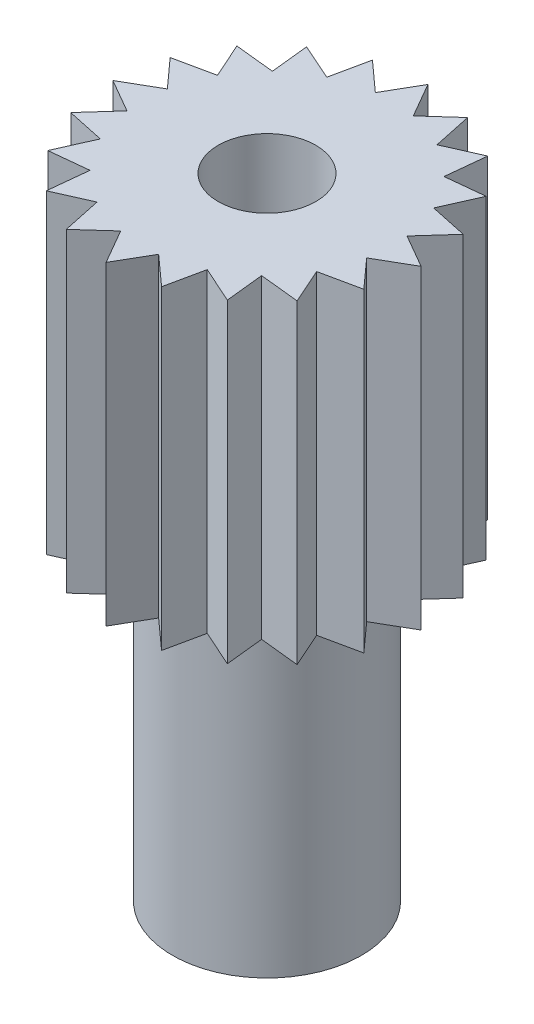
SolidWorks part; units mm, degrees
ref_plane "Front Plane" through (0, 0, 0) normal (0, 0, 1) x (1, 0, 0)
ref_plane "Top Plane" through (0, 0, 0) normal (0, 1, 0) x (1, 0, 0)
ref_plane "Right Plane" through (0, 0, 0) normal (1, 0, 0) x (0, 0, -1)
sketch "Sketch1" plane through (0, 0, 0) normal (0, 1, 0) x (1, 0, 0)
  circle A0 centre (0, 0) radius 3
  circle A1 centre (0, 0) radius 7
extrude "Boss-Extrude1" add sketch "Sketch1" along normal blind 20
sketch "Sketch2" plane through (0, 20, 0) normal (0, 1, 0) x (1, 0, 0)
  circle A0 centre (0, 0) radius 10
  circle A1 centre (0, 0) radius 3
extrude "Boss-Extrude2" add sketch "Sketch2" along normal blind 20
sketch "Sketch3" plane through (0, 40, 0) normal (0, 1, 0) x (1, 0, 0)
  line L0 (3.2961, 9.4437) -> (1.3653, 7.7052)
  line L1 (0.2165, 10) -> (-1.0825, 7.75)
  line L2 (-1.0825, 7.75) -> (1.5155, 7.75)
  line L3 (1.5155, 7.75) -> (0.2165, 10)
  line L4 (3.8363, 6.9024) -> (3.2961, 9.4437)
  line L5 (1.3653, 7.7052) -> (3.8363, 6.9024)
  line L6 (6.053, 7.9629) -> (3.6795, 6.9062)
  line L7 (5.7814, 5.3791) -> (6.053, 7.9629)
  line L8 (3.6795, 6.9062) -> (5.7814, 5.3791)
  line L9 (8.2174, 5.7027) -> (5.6336, 5.4311)
  line L10 (7.1607, 3.3292) -> (8.2174, 5.7027)
  line L11 (5.6336, 5.4311) -> (7.1607, 3.3292)
  line L12 (9.5775, 2.8843) -> (7.0362, 3.4244)
  line L13 (7.839, 0.9535) -> (9.5775, 2.8843)
  line L14 (7.0362, 3.4244) -> (7.839, 0.9535)
  line L15 (10, -0.2165) -> (7.75, 1.0825)
  line L16 (7.75, -1.5155) -> (10, -0.2165)
  line L17 (7.75, 1.0825) -> (7.75, -1.5155)
  line L18 (9.4437, -3.2961) -> (7.7052, -1.3653)
  line L19 (6.9024, -3.8363) -> (9.4437, -3.2961)
  line L20 (7.7052, -1.3653) -> (6.9024, -3.8363)
  line L21 (7.9629, -6.053) -> (6.9062, -3.6795)
  line L22 (5.3791, -5.7814) -> (7.9629, -6.053)
  line L23 (6.9062, -3.6795) -> (5.3791, -5.7814)
  line L24 (5.7027, -8.2174) -> (5.4311, -5.6336)
  line L25 (3.3292, -7.1607) -> (5.7027, -8.2174)
  line L26 (5.4311, -5.6336) -> (3.3292, -7.1607)
  line L27 (2.8843, -9.5775) -> (3.4244, -7.0362)
  line L28 (0.9535, -7.839) -> (2.8843, -9.5775)
  line L29 (3.4244, -7.0362) -> (0.9535, -7.839)
  line L30 (-0.2165, -10) -> (1.0825, -7.75)
  line L31 (-1.5155, -7.75) -> (-0.2165, -10)
  line L32 (1.0825, -7.75) -> (-1.5155, -7.75)
  line L33 (-3.2961, -9.4437) -> (-1.3653, -7.7052)
  line L34 (-3.8363, -6.9024) -> (-3.2961, -9.4437)
  line L35 (-1.3653, -7.7052) -> (-3.8363, -6.9024)
  line L36 (-6.053, -7.9629) -> (-3.6795, -6.9062)
  line L37 (-5.7814, -5.3791) -> (-6.053, -7.9629)
  line L38 (-3.6795, -6.9062) -> (-5.7814, -5.3791)
  line L39 (-8.2174, -5.7027) -> (-5.6336, -5.4311)
  line L40 (-7.1607, -3.3292) -> (-8.2174, -5.7027)
  line L41 (-5.6336, -5.4311) -> (-7.1607, -3.3292)
  line L42 (-9.5775, -2.8843) -> (-7.0362, -3.4244)
  line L43 (-7.839, -0.9535) -> (-9.5775, -2.8843)
  line L44 (-7.0362, -3.4244) -> (-7.839, -0.9535)
  line L45 (-10, 0.2165) -> (-7.75, -1.0825)
  line L46 (-7.75, 1.5155) -> (-10, 0.2165)
  line L47 (-7.75, -1.0825) -> (-7.75, 1.5155)
  line L48 (-9.4437, 3.2961) -> (-7.7052, 1.3653)
  line L49 (-6.9024, 3.8363) -> (-9.4437, 3.2961)
  line L50 (-7.7052, 1.3653) -> (-6.9024, 3.8363)
  line L51 (-7.9629, 6.053) -> (-6.9062, 3.6795)
  line L52 (-5.3791, 5.7814) -> (-7.9629, 6.053)
  line L53 (-6.9062, 3.6795) -> (-5.3791, 5.7814)
  line L54 (-5.7027, 8.2174) -> (-5.4311, 5.6336)
  line L55 (-3.3292, 7.1607) -> (-5.7027, 8.2174)
  line L56 (-5.4311, 5.6336) -> (-3.3292, 7.1607)
  line L57 (-2.8843, 9.5775) -> (-3.4244, 7.0362)
  line L58 (-0.9535, 7.839) -> (-2.8843, 9.5775)
  line L59 (-3.4244, 7.0362) -> (-0.9535, 7.839)
  circle A0 centre (0.2165, 8.5) radius 0.75 construction
  circle A2 centre (0, 0) radius 10
  point P65 (0, 0)
  dimension "D1" = 20
extrude "Cut-Extrude2" cut sketch "Sketch3" against normal blind 20 contours L48 L3 L46 | L51 L3 L49 | L54 L3 L52 | L45 L3 L43 | L42 L3 L40 | L39 L3 L37 | L36 L3 L34 | L33 L3 L31 | L30 L3 L28 | L27 L3 L25 | L24 L3 L22 | L21 L3 L19 | L18 L3 L16 | L15 L3 L13 | L12 L3 L10 | L9 L3 L7 | L6 L3 L4 | L3 L0 | L58 L1 L3 | L57 L3 L55
sketch "Sketch4" plane through (0, 0, 0) normal (0, -1, 0) x (-1, 0, 0)
  circle A0 centre (0, 0) radius 6
  circle A1 centre (3.2447, 1.1922) radius 21.6552
extrude "Cut-Extrude3" cut sketch "Sketch4" against normal blind 20
sketch "Sketch6" plane through (0, 0, 0) normal (0, -1, 0) x (-1, 0, 0)
  circle A0 centre (0, 0) radius 3.1
extrude "Cut-Extrude4" cut sketch "Sketch6" against normal blind 80
